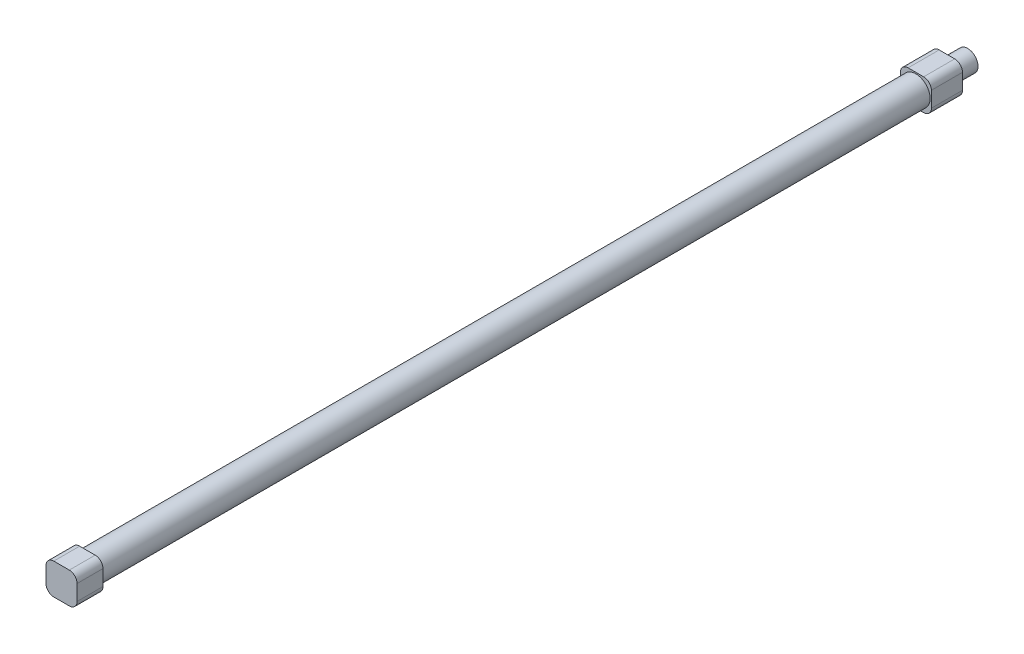
SolidWorks part; units mm, degrees
ref_plane "前视基准面" through (0, 0, 0) normal (0, 0, 1) x (1, 0, 0)
ref_plane "上视基准面" through (0, 0, 0) normal (0, 1, 0) x (1, 0, 0)
ref_plane "右视基准面" through (0, 0, 0) normal (1, 0, 0) x (0, 0, -1)
sketch "草图1" plane through (0, 0, 0) normal (0, 0, 1) x (1, 0, 0)
  circle A0 centre (0, 0) radius 5.5
  circle A1 centre (0, 0) radius 5
extrude "凸台-拉伸1" add sketch "草图1" along normal blind 320
sketch "草图2" plane through (0, 0, 320) normal (0, 0, 1) x (1, 0, 0)
  line L1 (-3, -6) -> (3, -6)
  line L2 (-6, -3) -> (-6, 3)
  line L3 (-3, 6) -> (3, 6)
  line L4 (6, -3) -> (6, 3)
  line L5 (-6, -6) -> (6, 6) construction
  line L6 (-6, 6) -> (6, -6) construction
  arc A0 (-3, 6) -> (-6, 3) centre (-3, 3) ccw
  arc A1 (6, 3) -> (3, 6) centre (3, 3) ccw
  arc A2 (6, -3) -> (3, -6) centre (3, -3) cw
  arc A3 (-6, -3) -> (-3, -6) centre (-3, -3) ccw
  point P0 (0, 0)
  dimension "D3" = 3
  dimension "D4" = 3
  dimension "D5" = 3
  dimension "D6" = 3
  dimension "D1" = 12
  dimension "D2" = 12
extrude "凸台-拉伸2" add sketch "草图2" along normal blind 10
sketch "草图3" plane through (0, 0, 0) normal (0, 0, -1) x (-1, 0, 0)
  line L1 (-3, -6) -> (3, -6)
  line L2 (-6, -3) -> (-6, 3)
  line L3 (-3, 6) -> (3, 6)
  line L4 (6, -3) -> (6, 3)
  line L5 (-6, -6) -> (6, 6) construction
  line L6 (-6, 6) -> (6, -6) construction
  arc A0 (-6, -3) -> (-3, -6) centre (-3, -3) ccw
  arc A1 (3, -6) -> (6, -3) centre (3, -3) ccw
  arc A2 (6, 3) -> (3, 6) centre (3, 3) ccw
  arc A3 (-3, 6) -> (-6, 3) centre (-3, 3) ccw
  point P0 (0, 0)
  dimension "D3" = 3
  dimension "D1" = 12
  dimension "D2" = 12
extrude "凸台-拉伸3" add sketch "草图3" along normal blind 12
sketch "草图4" plane through (0, 0, -12) normal (0, 0, -1) x (-1, 0, 0)
  circle A0 centre (0, 0) radius 4
extrude "凸台-拉伸4" add sketch "草图4" along normal blind 8
sketch "草图5" plane through (0, 0, -20) normal (0, 0, -1) x (-1, 0, 0)
  circle A0 centre (0, 0) radius 2
extrude "切除-拉伸1" cut sketch "草图5" against normal blind 38
sketch "草图6" plane through (-6, 0, 0) normal (-1, 0, 0) x (0, 0, 1)
  line L0 (0, -5.5) -> (0, 5.5) construction
  line L1 (320, 3) -> (320, -3) construction
  circle A0 centre (-4, 0) radius 2
  circle A1 centre (324, 0) radius 2
  point P6 (320, 0)
  dimension "D1" = 4
  dimension "D2" = 4
extrude "切除-拉伸3" cut sketch "草图6" against normal blind 3
